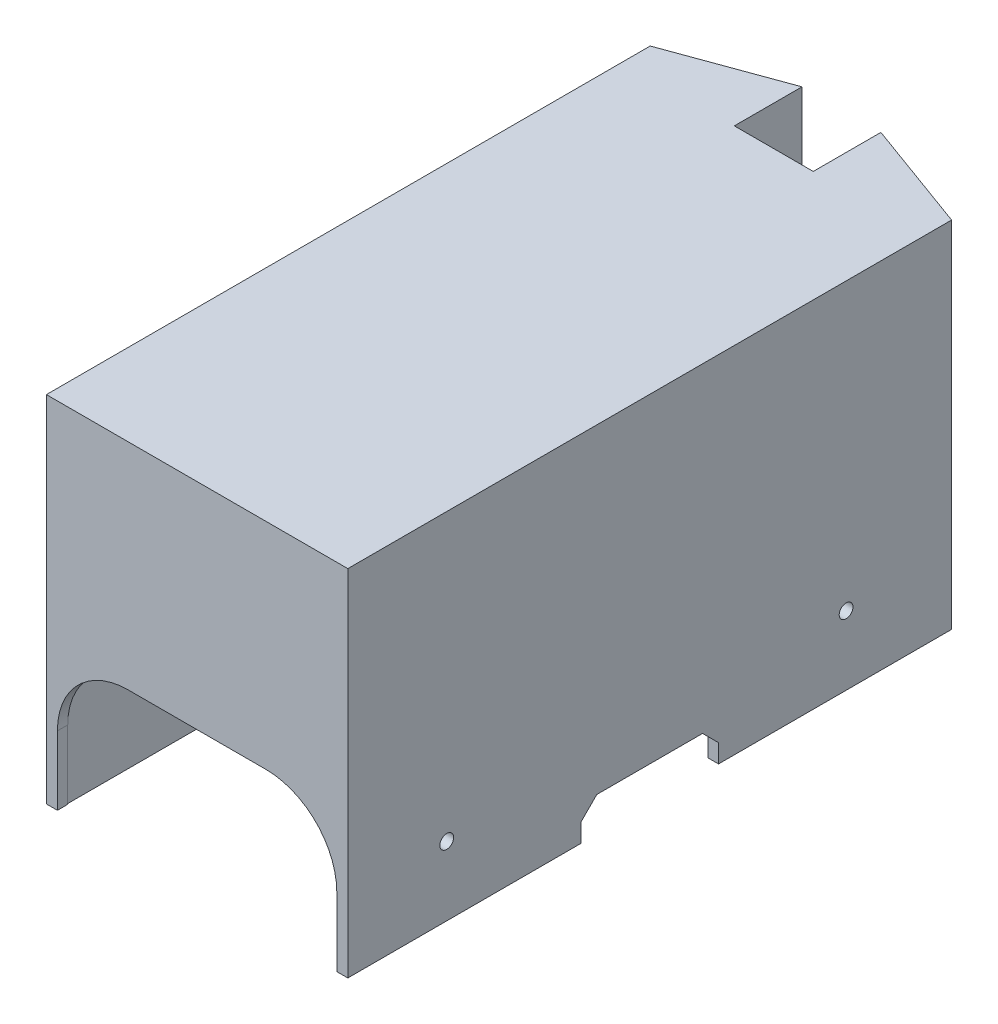
SolidWorks part; units mm, degrees
ref_plane "Front Plane" through (0, 0, 0) normal (0, 0, 1) x (1, 0, 0)
ref_plane "Top Plane" through (0, 0, 0) normal (0, 1, 0) x (1, 0, 0)
ref_plane "Right Plane" through (0, 0, 0) normal (1, 0, 0) x (0, 0, -1)
sketch "Sketch1" plane through (0, 0, 0) normal (0, 1, 0) x (1, 0, 0)
  line L8 (-21.4352, -43.5768) -> (19.3648, -43.5768)
  line L9 (19.3648, -43.5768) -> (19.3648, 41.611)
  line L10 (19.3648, 41.611) -> (6.1982, 46.4104)
  line L11 (6.1982, 46.4104) -> (6.1982, 37.2232)
  line L12 (6.1982, 37.2232) -> (-8.2687, 37.2232)
  line L13 (-8.2687, 37.2232) -> (-8.2687, 46.4104)
  line L14 (-8.2687, 46.4104) -> (-21.4352, 41.611)
  line L15 (-21.4352, 41.611) -> (-21.4352, -43.5768)
  line L16 (-22.9352, -45.0768) -> (20.8648, -45.0768)
  line L17 (20.8648, -45.0768) -> (20.8648, 42.6607)
  line L18 (20.8648, 42.6607) -> (4.6982, 48.5537)
  line L19 (4.6982, 48.5537) -> (4.6982, 38.7232)
  line L20 (4.6982, 38.7232) -> (-6.7687, 38.7232)
  line L21 (-6.7687, 38.7232) -> (-6.7687, 48.5537)
  line L22 (-6.7687, 48.5537) -> (-22.9352, 42.6607)
  line L23 (-22.9352, 42.6607) -> (-22.9352, -45.0768)
  dimension "D1" = 1.5
extrude "Boss-Extrude1" add sketch "Sketch1" along normal blind 50
sketch "Sketch2" plane through (0, 50, 0) normal (0, 1, 0) x (1, 0, 0)
  line L8 (-22.9352, 42.6607) -> (-22.9352, -45.0768)
  line L9 (-22.9352, -45.0768) -> (20.8648, -45.0768)
  line L10 (20.8648, -45.0768) -> (20.8648, 42.6607)
  line L11 (20.8648, 42.6607) -> (4.6982, 48.5537)
  line L12 (4.6982, 48.5537) -> (4.6982, 38.7232)
  line L13 (4.6982, 38.7232) -> (-6.7687, 38.7232)
  line L14 (-6.7687, 38.7232) -> (-6.7687, 48.5537)
  line L15 (-6.7687, 48.5537) -> (-22.9352, 42.6607)
  line L16 (-22.9352, 42.6607) -> (-22.9352, -45.0768)
  line L17 (-22.9352, -45.0768) -> (20.8648, -45.0768)
  line L18 (20.8648, -45.0768) -> (20.8648, 42.6607)
  line L19 (20.8648, 42.6607) -> (4.6982, 48.5537)
  line L20 (4.6982, 48.5537) -> (4.6982, 38.7232)
  line L21 (4.6982, 38.7232) -> (-6.7687, 38.7232)
  line L22 (-6.7687, 38.7232) -> (-6.7687, 48.5537)
  line L23 (-6.7687, 48.5537) -> (-22.9352, 42.6607)
  dimension "D1" = 0
extrude "Boss-Extrude2" add sketch "Sketch2" along normal blind 1.52
sketch "Sketch3" plane through (0, 0, 45.0768) normal (0, 0, 1) x (1, 0, 0)
  line L1 (-21.0352, 10) -> (-21.0352, 0)
  line L2 (-21.0352, 0) -> (18.9648, 0)
  line L3 (18.9648, 0) -> (18.9648, 10)
  line L4 (-22.9352, 0) -> (20.8648, 0) construction
  line L5 (8.9648, 20.3) -> (-11.0352, 20.3)
  line L6 (-21.3352, 10) -> (-21.3352, -0.3)
  line L7 (-21.3352, -0.3) -> (19.2648, -0.3)
  line L8 (19.2648, -0.3) -> (19.2648, 10)
  line L9 (8.9648, 20) -> (-11.0352, 20) construction
  arc A0 (18.9648, 10) -> (8.9648, 20) centre (8.9648, 10) ccw
  arc A1 (-11.0352, 20) -> (-21.0352, 10) centre (-11.0352, 10) ccw
  arc A4 (-11.0352, 20.3) -> (-21.3352, 10) centre (-11.0352, 10) ccw
  arc A5 (19.2648, 10) -> (8.9648, 20.3) centre (8.9648, 10) ccw
  point P12 (-1.0352, 0)
  point P13 (-1.0352, 0)
  line M1 (-22.9352, 0) -> (20.8648, 0)
  dimension "D1" = 0.3
extrude "Cut-Extrude2" cut sketch "Sketch3" against normal blind 1.52 contours A0 L9 A1 L1 L3 M1 | L9 A0 L3 L8 A5 L5 A4 L6 L1 A1 M1
sketch "Sketch4" plane through (20.8648, 0, 0) normal (1, 0, 0) x (0, 0, -1)
  line L0 (-32.395, 10) -> (-33.395, 10) construction
  line L1 (-28.395, 10) -> (-30.395, 10) construction
  line L2 (-45.9619, 10) -> (-45.9619, 0)
  line L3 (-45.9619, 0) -> (-45.0768, 0)
  line L4 (43.5459, 0) -> (43.5459, 5)
  line L6 (-40.9619, 5) -> (-40.9619, 10)
  line L8 (42.6607, 0) -> (43.5459, 0)
  line L9 (29.6381, 10) -> (27.6381, 10) construction
  line L10 (25.6381, 10) -> (24.6381, 10) construction
  circle A6 centre (25.6381, 10) radius 1
  circle A7 centre (-32.395, 10) radius 1
  circle A8 centre (-30.7036, 10) radius 1
  circle A9 centre (27.3296, 10) radius 1
  point P12 (-1.208, 0)
  point P13 (1.292, 5)
  point P14 (-1.208, 0)
  dimension "D1" = 5
  dimension "D2" = 5
extrude "Cut-Extrude8" cut sketch "Sketch4" against normal blind 178.52 contours A7 A8 | A7 A8 | A6 A9 | A6 A9
sketch "Sketch5" plane through (20.8648, 0, 0) normal (1, 0, 0) x (0, 0, -1)
  line L0 (-45.0768, 0) -> (42.6607, 0) construction
  line L1 (-45.0768, 0) -> (42.6607, 0)
  line L2 (-8.8919, 5) -> (-11.208, 2.6838)
  line L3 (-11.208, 5) -> (8.792, 5)
  line L4 (-11.208, 5) -> (-11.208, -5)
  line L5 (-11.208, -5) -> (8.792, -5)
  line L6 (8.792, 5) -> (8.792, -5)
  line L7 (-1.208, -5) -> (-1.208, 5) construction
  line L8 (-11.208, 0) -> (8.792, 0) construction
  line L9 (6.4758, 5) -> (8.792, 2.6838)
  point P2 (-1.208, 0)
  dimension "D1" = 20
  dimension "D2" = 5
extrude "Cut-Extrude9" cut sketch "Sketch5" against normal blind 178.52 contours L9 L3 L2 L4 L1 L6
